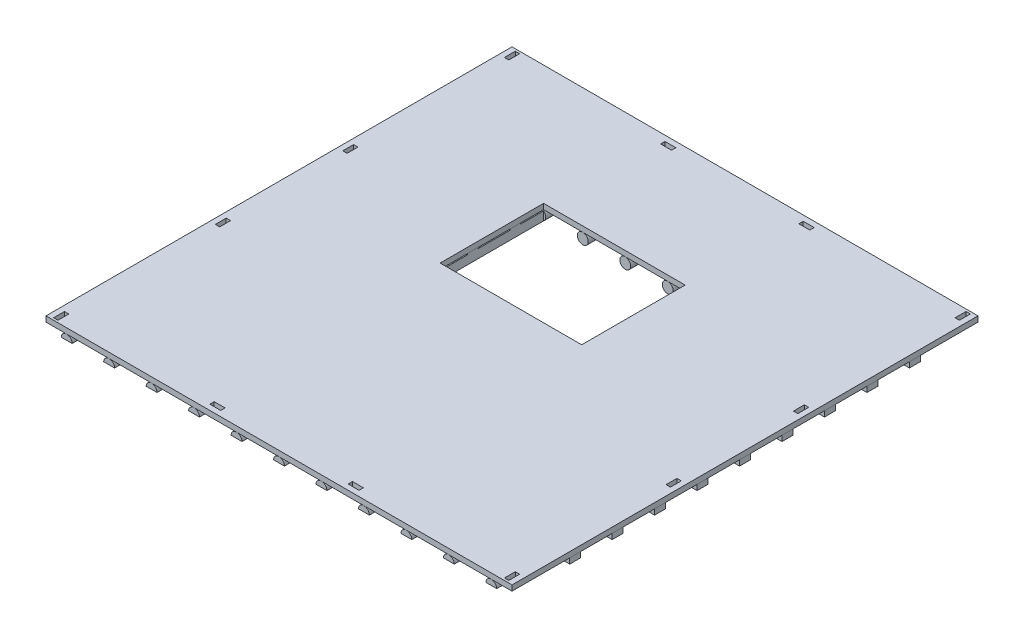
SolidWorks part; units mm, degrees
material "松木"
ref_plane "前视基准面" through (0, 0, 0) normal (0, 0, 1) x (1, 0, 0)
ref_plane "上视基准面" through (0, 0, 0) normal (0, 1, 0) x (1, 0, 0)
ref_plane "右视基准面" through (0, 0, 0) normal (1, 0, 0) x (0, 0, -1)
sketch "草图1" plane through (0, 0, 0) normal (0, 1, 0) x (1, 0, 0)
  line L1 (0, 0) -> (4280, 0)
  line L2 (0, 0) -> (0, 4280)
  line L3 (0, 4280) -> (4280, 4280)
  line L4 (4280, 0) -> (4280, 4280)
  dimension "D1" = 4280
  dimension "D2" = 4280
extrude "凸台-拉伸1" add sketch "草图1" along normal blind 50 contours L2 L1 L4 L3
sketch "草图2" plane through (0, 0, 0) normal (0, 0, 1) x (1, 0, 0)
  line L0 (0, 0) -> (140, 0)
  line L1 (0, 0) -> (4280, 0) construction
  circle A0 centre (190, -50) radius 50
  dimension "D2" = 100
  dimension "D1" = 140
  dimension "D3" = 50
extrude "凸台-拉伸3" add sketch "草图2" against normal blind 4280 separate body contours A0
sketch "草图3" plane through (0, 0, 0) normal (0, 0, 1) x (1, 0, 0)
  line L0 (0, 0) -> (4280, 0) construction
  line L1 (140, -50) -> (240, -50)
  line L2 (140, -50) -> (140, -150)
  line L3 (140, -150) -> (240, -150)
  line L4 (240, -50) -> (240, -150)
  dimension "D1" = 100
  dimension "D2" = 100
  dimension "D3" = 140
  dimension "D4" = 50
extrude "切除-拉伸1" cut sketch "草图3" against normal blind 140
sketch "草图4" plane through (0, 0, -4280) normal (0, 0, -1) x (-1, 0, 0)
  line L0 (0, 0) -> (-4280, 0) construction
  line L1 (-240, -150) -> (-140, -150)
  line L2 (-240, -150) -> (-240, -50)
  line L3 (-240, -50) -> (-140, -50)
  line L4 (-140, -150) -> (-140, -50)
  dimension "D1" = 100
  dimension "D2" = 100
  dimension "D3" = 50
  dimension "D4" = 140
extrude "切除-拉伸2" cut sketch "草图4" against normal blind 140
pattern_linear "阵列(线性)2" count 11 spacing 390 along (1, 0, 0) of "凸台-拉伸3", "切除-拉伸1", "切除-拉伸2"
sketch "草图5" plane through (4280, 0, 0) normal (1, 0, 0) x (0, 0, -1)
  line L0 (0, 0) -> (4280, 0) construction
  line L1 (530, 0) -> (630, 0)
  line L2 (530, 0) -> (530, -30)
  line L3 (530, -30) -> (630, -30)
  line L4 (630, 0) -> (630, -30)
  dimension "D1" = 530
  dimension "D2" = 30
  dimension "D3" = 100
extrude "切除-拉伸3" cut sketch "草图5" against normal blind 4280
sketch "草图6" plane through (4280, 0, 0) normal (1, 0, 0) x (0, 0, -1)
  line L1 (630, -30) -> (530, -30)
  line L2 (630, -30) -> (630, -0.01)
  line L3 (630, -0.01) -> (530, -0.01)
  line L4 (530, -30) -> (530, -0.01)
  line L7 (0, 50) -> (4280, 50) construction
  dimension "D1" = 100
  dimension "D2" = 29.99
  dimension "D3" = 530
  dimension "D4" = 50.01
extrude "凸台-拉伸6" add sketch "草图6" against normal blind 4280
sketch "草图7" plane through (0, -30, 0) normal (0, -1, 0) x (1, 0, 0)
  line L0 (4135.8258, -530) -> (4280, -530) construction
  line L1 (4280, -630) -> (4180, -630)
  line L2 (4280, -630) -> (4280, -530)
  line L3 (4280, -530) -> (4180, -530)
  line L4 (4180, -630) -> (4180, -530)
  dimension "D1" = 100
extrude "凸台-拉伸9" add sketch "草图7" along normal blind 20 contours L2 L1 L4 L3
sketch "草图8" plane through (0, -30, 0) normal (0, -1, 0) x (1, 0, 0)
  line L0 (0, -530) -> (144.1742, -530) construction
  line L1 (0, -630) -> (100, -630)
  line L2 (0, -630) -> (0, -530)
  line L3 (0, -530) -> (100, -530)
  line L4 (100, -630) -> (100, -530)
  dimension "D1" = 100
extrude "凸台-拉伸10" add sketch "草图8" along normal blind 20
pattern_linear "阵列(线性)3" count 9 spacing 390 along (0, 0, -1) of "凸台-拉伸10", "凸台-拉伸9", "凸台-拉伸6"
sketch "草图9" plane through (0, 0, 0) normal (0, -1, 0) x (1, 0, 0)
  line L0 (0, 0) -> (0, -4280) construction
  line L1 (50, -120) -> (90, -120)
  line L2 (50, -120) -> (50, -20)
  line L3 (50, -20) -> (90, -20)
  line L4 (90, -120) -> (90, -20)
  line L5 (0, 0) -> (4280, 0) construction
  dimension "D1" = 100
  dimension "D2" = 40
  dimension "D3" = 50
  dimension "D4" = 20
extrude "切除-拉伸4" cut sketch "草图9" against normal through all
pattern_linear "阵列(线性)4" count 2 spacing 4140 along (1, 0, 0) count 2 spacing 4140 along (0, 0, -1) of "切除-拉伸4"
sketch "草图10" plane through (0, 0, 0) normal (0, -1, 0) x (1, 0, 0)
  line L0 (0, 0) -> (0, -4280) construction
  line L1 (50, -1505) -> (90, -1505)
  line L2 (50, -1505) -> (50, -1605)
  line L3 (50, -1605) -> (90, -1605)
  line L4 (90, -1505) -> (90, -1605)
  line L5 (0, 0) -> (4280, 0) construction
  dimension "D1" = 100
  dimension "D2" = 40
  dimension "D3" = 50
  dimension "D4" = 1505
extrude "切除-拉伸5" cut sketch "草图10" against normal through all
pattern_linear "阵列(线性)5" count 2 spacing 4140 along (1, 0, 0) of "切除-拉伸5"
pattern_linear "阵列(线性)6" count 2 spacing 1170 along (0, 0, -1) of "阵列(线性)5"
sketch "草图11" plane through (0, 0, 0) normal (0, -1, 0) x (1, 0, 0)
  line L0 (0, 0) -> (4280, 0) construction
  line L1 (1555, -90) -> (1455, -90)
  line L2 (1555, -90) -> (1555, -50)
  line L3 (1555, -50) -> (1455, -50)
  line L4 (1455, -90) -> (1455, -50)
  line L5 (0, 0) -> (0, -4280) construction
  dimension "D1" = 100
  dimension "D2" = 40
  dimension "D3" = 50
  dimension "D4" = 1455
extrude "切除-拉伸6" cut sketch "草图11" against normal blind 100
pattern_linear "阵列(线性)7" count 2 spacing 1270 along (1, 0, 0) count 2 spacing 4140 along (0, 0, -1) of "切除-拉伸6"
sketch "草图12" plane through (0, 50, 0) normal (0, 1, 0) x (1, 0, 0)
  line L0 (0, 4280) -> (4280, 4280) construction
  line L1 (140, 4140) -> (1390, 4140)
  line L2 (140, 4140) -> (140, 2230)
  line L3 (140, 2230) -> (1390, 2230)
  line L4 (1390, 4140) -> (1390, 2230)
  line L6 (0, 0) -> (0, 4280) construction
  line L8 (1390, 2230) -> (440, 2230)
  line L9 (1390, 2230) -> (1390, 465)
  line L10 (1390, 465) -> (440, 465)
  line L11 (440, 2230) -> (440, 465)
  line L12 (1390, 2230) -> (2690, 2230)
  line L13 (1390, 2230) -> (1390, 3180)
  line L14 (1390, 3180) -> (2690, 3180)
  line L15 (2690, 2230) -> (2690, 3180)
  dimension "D1" = 1250
  dimension "D2" = 140
  dimension "D3" = 140
  dimension "D4" = 1910
  dimension "D5" = 1765
  dimension "D6" = 950
  dimension "D7" = 1300
  dimension "D8" = 950
extrude "切除-拉伸7" cut sketch "草图12" against normal through all contours L12 L15 L14 L4
